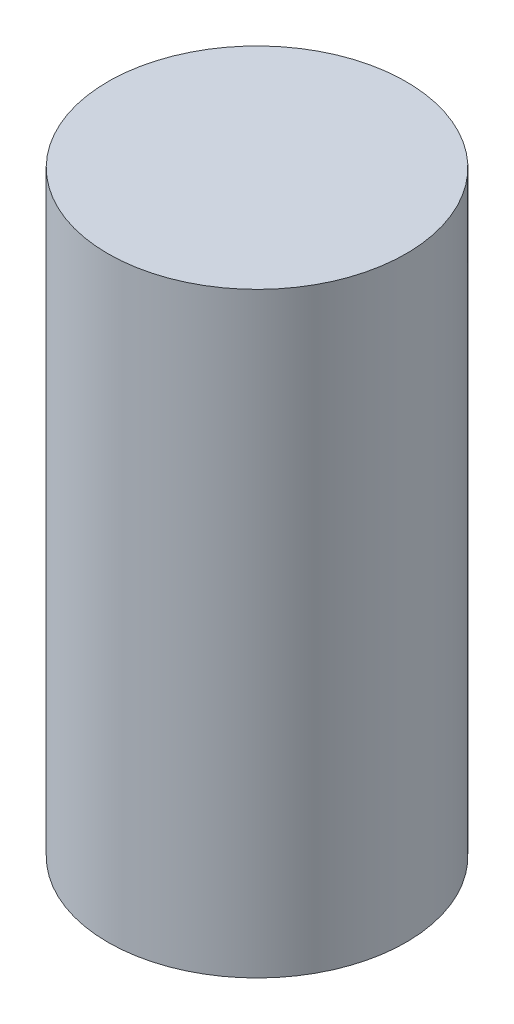
SolidWorks part; units mm, degrees
ref_plane "Front Plane" through (0, 0, 0) normal (0, 0, 1) x (1, 0, 0)
ref_plane "Top Plane" through (0, 0, 0) normal (0, 1, 0) x (1, 0, 0)
ref_plane "Right Plane" through (0, 0, 0) normal (1, 0, 0) x (0, 0, -1)
sketch "Sketch1" plane through (0, 0, 0) normal (0, 1, 0) x (1, 0, 0)
  circle A0 centre (0, 0) radius 15.24
  dimension "D1" = 30.48
extrude "Boss-Extrude1" add sketch "Sketch1" along normal blind 60.96
